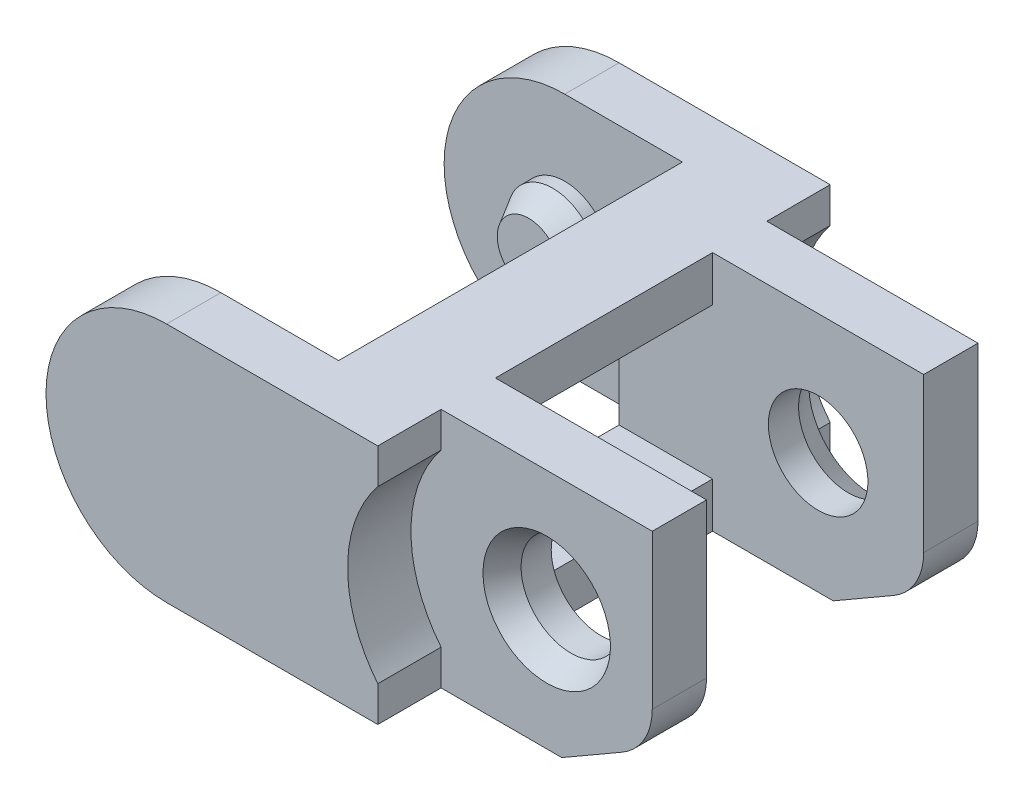
SolidWorks part; units mm, degrees
ref_plane "Plano frontal" through (0, 0, 0) normal (0, 0, 1) x (1, 0, 0)
ref_plane "Plano superior" through (0, 0, 0) normal (0, 1, 0) x (1, 0, 0)
ref_plane "Plano direito" through (0, 0, 0) normal (1, 0, 0) x (0, 0, -1)
sketch "Esboço1" plane through (0, 0, 0) normal (0, 0, 1) x (1, 0, 0)
  line L0 (-7, 0) -> (7, 0)
  line L1 (7, 0) -> (7, -6.2679)
  line L2 (7, -6.2679) -> (4, -8)
  line L3 (4, -8) -> (-7, -8)
  arc A0 (-7, 0) -> (-7, -8) centre (-7, -4) ccw
  circle A1 centre (4.2, -4) radius 1.5312 construction
  point P7 (0, 0)
  dimension "D1" = 4
  dimension "D2" = 14
  dimension "D3" = 30
  dimension "D4" = 11
  dimension "D5" = 2.8
extrude "Ressalto-extrusão1" add sketch "Esboço1" along normal mid plane 15
sketch "Esboço2" plane through (0, 0, 0) normal (0, 1, 0) x (1, 0, 0)
  line L0 (-11, 5.7) -> (-3.1, 5.7)
  line L1 (-11, 7.5) -> (-11, -7.5) construction
  line L2 (-3.1, 5.7) -> (-3.1, -5.7)
  line L3 (-3.1, -5.7) -> (-11, -5.7)
  line L4 (-11, 5.7) -> (-11, -5.7)
  line L5 (7, 0) -> (-9.8604, 0) construction
  line L6 (7, -7.5) -> (7, 7.5) construction
  line L7 (-11, -7.5) -> (-7, -7.5) construction
  line L8 (7, -5.4) -> (0, -5.4)
  line L9 (0, -5.4) -> (0, -7.5)
  line L10 (7, -7.5) -> (-7, -7.5) construction
  line L11 (0, -7.5) -> (7, -7.5)
  line L12 (7, -7.5) -> (7, -5.4)
  line L13 (7, 7.5) -> (7, 5.4)
  line L14 (0, 7.5) -> (7, 7.5)
  line L15 (0, 5.4) -> (0, 7.5)
  line L16 (7, 5.4) -> (0, 5.4)
  line L18 (7, 3.6) -> (0, 3.6)
  line L19 (7, 3.6) -> (7, -3.6)
  line L20 (7, -3.6) -> (0, -3.6)
  line L21 (0, 3.6) -> (0, -3.6)
  point P10 (-11, 0)
  point P28 (0, 0)
  dimension "D1" = 1.8
  dimension "D3" = 2.1
  dimension "D4" = 7
  dimension "D5" = 1.8
  dimension "D2" = 3.1
extrude "Corte-extrusão1" cut sketch "Esboço2" against normal through all both and the other way through all
sketch "Esboço3" plane through (0, 0, 0) normal (1, 0, 0) x (0, 0, -1)
  line L0 (-3.6, -6.2679) -> (-3.6, 0) construction
  line L1 (-3.6, -1.5) -> (3.6, -1.5)
  line L2 (-3.6, -1.5) -> (-3.6, -6.5)
  line L3 (-3.6, -6.5) -> (3.6, -6.5)
  line L4 (3.6, -1.5) -> (3.6, -6.5)
  line L5 (3.6, -6.2679) -> (3.6, -8) construction
  line L8 (-3.6, 0) -> (3.6, 0) construction
  line L9 (3.6, -8) -> (-3.6, -8) construction
  dimension "D1" = 1.5
  dimension "D2" = 1.5
extrude "Corte-extrusão2" cut sketch "Esboço3" against normal through all both and the other way through all
sketch "Esboço4" plane through (0, 0, -5.4) normal (0, 0, -1) x (-1, 0, 0)
  line L0 (-7, -6.2679) -> (-7, 0) construction
  circle A0 centre (-3.5, -4) radius 1.65
  circle A1 centre (7, -4) radius 1.65 construction
  dimension "D1" = 3.3
  dimension "D2" = 3.5
extrude "Corte-extrusão3" cut sketch "Esboço4" against normal through all both and the other way through all
sketch "Esboço5" plane through (0, 0, 5.7) normal (0, 0, -1) x (-1, 0, 0)
  circle A0 centre (7, -4) radius 1.5
  dimension "D1" = 3
extrude "Ressalto-extrusão2" add sketch "Esboço5" along normal blind 1.2
sketch "Esboço6" plane through (0, 0, 7.5) normal (0, 0, 1) x (1, 0, 0)
  circle A0 centre (3.5, -4) radius 4.5
  dimension "D1" = 9
extrude "Corte-extrusão4" cut sketch "Esboço6" against normal blind 2.1
mirror "Espelhar1" about plane through (0, 0, 0) normal (0, 0, 1) of "Ressalto-extrusão2", "Corte-extrusão4"
fillet "Filete1" radius 2 2 edges at (7, -6.2679, -4.5) (7, -6.2679, 4.5)
chamfer "Chanfro1" distance 0.8 angle 30 4 edges at (-8.5, -4, 4.5) (-8.5, -4, -4.5) (1.85, -4, 5.4) (5.15, -4, -5.4)
equation "\"D5@Esboço2\"=\"D1@Esboço2\""
equation "\"D3@Esboço2\"=\"D1@Esboço2\"+0.3"
